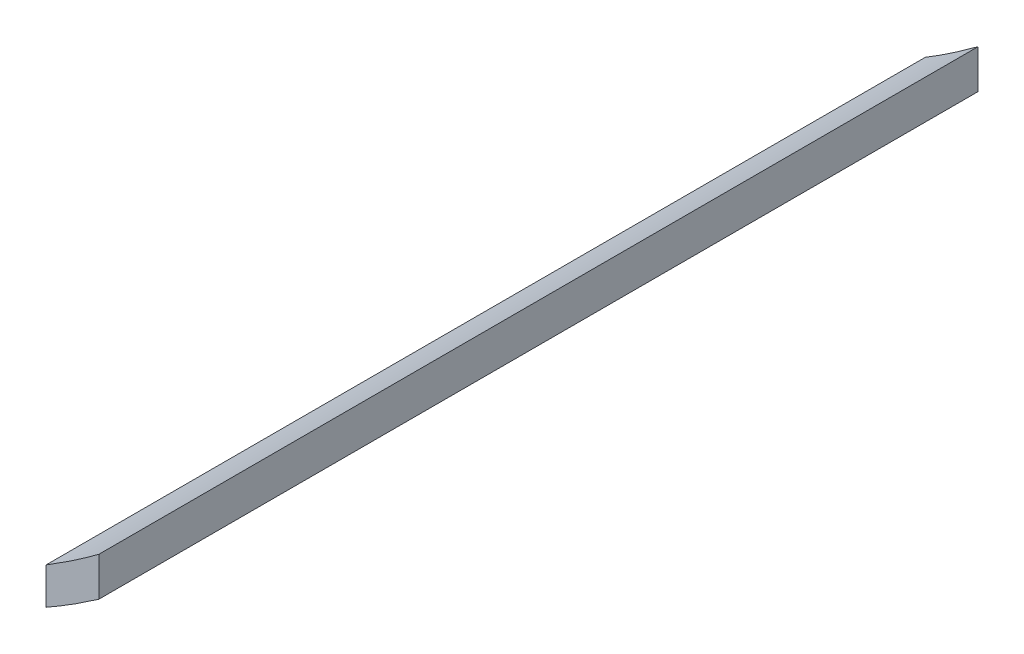
SolidWorks part; units mm, degrees
ref_plane "Front Plane" through (0, 0, 0) normal (0, 0, 1) x (1, 0, 0)
ref_plane "Top Plane" through (0, 0, 0) normal (0, 1, 0) x (1, 0, 0)
ref_plane "Right Plane" through (0, 0, 0) normal (1, 0, 0) x (0, 0, -1)
sketch "Sketch1" plane through (0, 0, 0) normal (0, 0, 1) x (1, 0, 0)
  line L16 (124.7026, -48.5426) -> (124.7026, -50.7562)
  line L17 (121.7026, -50.5645) -> (121.7026, -52.6501)
  spline S12 degree 3 poles (121.7026, -52.6501) (122.1433, -52.4015) (122.5781, -52.1428) (123.5814, -51.5172) (124.1462, -51.1431) (124.7026, -50.7562) knots 0.649205 0.649205 0.649205 0.649205 0.75 0.75 0.885223 0.885223 0.885223 0.885223
  spline S13 degree 3 poles (124.7026, -48.5426) (124.14, -48.957) (123.5691, -49.3594) (122.5653, -50.0277) (122.1372, -50.3009) (121.7026, -50.5645) knots 0.114062 0.114062 0.114062 0.114062 0.25 0.25 0.348788 0.348788 0.348788 0.348788
  dimension "D6" = 3
extrude "Boss-Extrude1" add sketch "Sketch1" along normal blind 50
